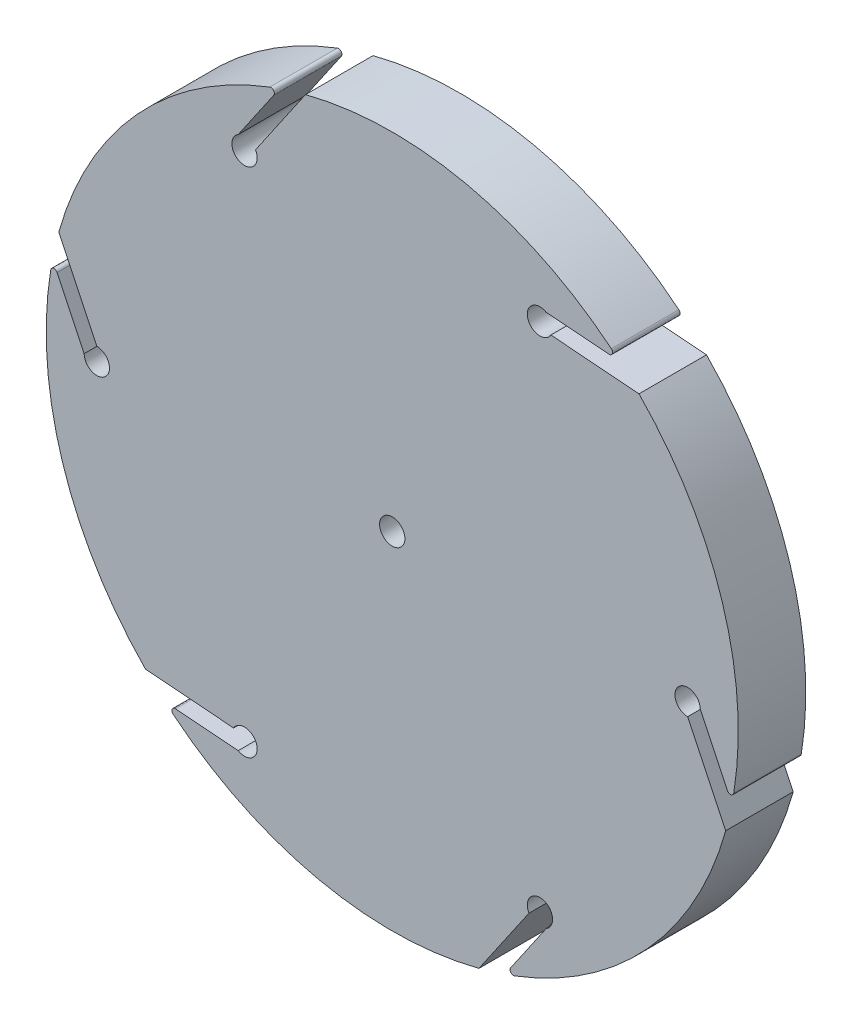
SolidWorks part; units mm, degrees
material "ABS"
ref_plane "Front Plane" through (0, 0, 0) normal (0, 0, 1) x (1, 0, 0)
ref_plane "Top Plane" through (0, 0, 0) normal (0, 1, 0) x (1, 0, 0)
ref_plane "Right Plane" through (0, 0, 0) normal (1, 0, 0) x (0, 0, -1)
sketch "Model" plane through (0, 0, 0) normal (0, 0, 1) x (1, 0, 0)
  circle A0 centre (-8.75, 15.1554) radius 0.75
  circle A1 centre (8.75, 15.1554) radius 0.75
  circle A2 centre (17.5, 0) radius 0.75
  circle A3 centre (8.75, -15.1554) radius 0.75
  circle A4 centre (-8.75, -15.1554) radius 0.75
  circle A224 centre (0, 0) radius 0.75
  circle A228 centre (-17.5, 0) radius 0.75
  circle A231 centre (0, 0) radius 20.5
  point P13 (0, 0)
  dimension "D1" = 41
  dimension "D2" = 1.5
  dimension "D3" = 17.5
  dimension "D4" = 6
extrude "Main Differential Disk" add sketch "Model" along normal blind 4
sketch "Sketch1" plane through (0, 0, 4) normal (0, 0, 1) x (1, 0, 0)
  line L0 (-18.25, 0) -> (-20.1218, 3.9193)
  line L1 (-17.5, 0.75) -> (-19.7558, 5.4733)
  line L2 (-9.125, 15.805) -> (-6.6667, 19.3857)
  line L3 (-8.1005, 15.5304) -> (-5.1379, 19.8457)
  line L4 (9.125, 15.805) -> (13.4552, 15.4664)
  line L5 (9.3995, 14.7804) -> (14.618, 14.3724)
  line L6 (18.25, 0) -> (20.1218, -3.9193)
  line L7 (17.5, -0.75) -> (19.7558, -5.4733)
  line L8 (9.125, -15.805) -> (6.6667, -19.3857)
  line L9 (8.1005, -15.5304) -> (5.1379, -19.8457)
  line L10 (-9.125, -15.805) -> (-13.4552, -15.4664)
  line L11 (-9.3995, -14.7804) -> (-14.618, -14.3724)
  arc A0 (-18.25, 0) -> (-17.5, 0.75) centre (-17.5, 0) ccw
  circle A1 centre (-17.5, 0) radius 0.75 construction
  circle A3 centre (0, 0) radius 20.5 construction
  arc A4 (-19.7558, 5.4733) -> (-20.1218, 3.9193) centre (0, 0) ccw
  arc A5 (-5.1379, 19.8457) -> (-6.6667, 19.3857) centre (0, 0) ccw
  arc A6 (-9.125, 15.805) -> (-8.1005, 15.5304) centre (-8.75, 15.1554) ccw
  arc A7 (14.618, 14.3724) -> (13.4552, 15.4664) centre (0, 0) ccw
  arc A8 (9.125, 15.805) -> (9.3995, 14.7804) centre (8.75, 15.1554) ccw
  arc A9 (19.7558, -5.4733) -> (20.1218, -3.9193) centre (0, 0) ccw
  arc A10 (18.25, 0) -> (17.5, -0.75) centre (17.5, 0) ccw
  arc A11 (5.1379, -19.8457) -> (6.6667, -19.3857) centre (0, 0) ccw
  arc A12 (9.125, -15.805) -> (8.1005, -15.5304) centre (8.75, -15.1554) ccw
  arc A13 (-14.618, -14.3724) -> (-13.4552, -15.4664) centre (0, 0) ccw
  arc A14 (-9.125, -15.805) -> (-9.3995, -14.7804) centre (-8.75, -15.1554) ccw
  point P39 (0, 0)
  dimension "D1" = 1
  dimension "D2" = 6
extrude "Tendon Holder" cut sketch "Sketch1" against normal through all
fillet "Differential Disk Contouring" radius 0.2 6 edges at (-20.1218, 3.9193, 2) (-13.4552, -15.4664, 2) (6.6667, -19.3857, 2) (20.1218, -3.9193, 2) (13.4552, 15.4664, 2) (-6.6667, 19.3857, 2)
